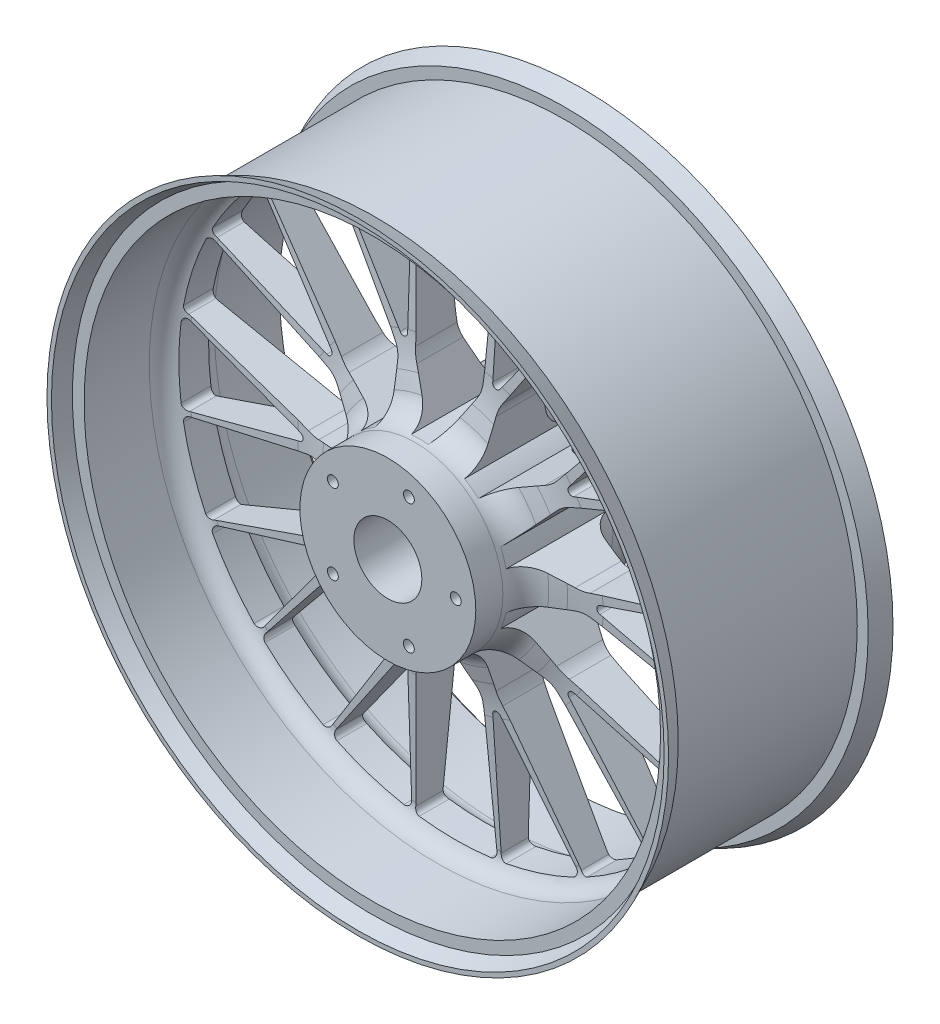
SolidWorks part; units mm, degrees
material "7050-T7651"
ref_plane "Front Plane" through (0, 0, 0) normal (0, 0, 1) x (1, 0, 0)
ref_plane "Top Plane" through (0, 0, 0) normal (0, 1, 0) x (1, 0, 0)
ref_plane "Right Plane" through (0, 0, 0) normal (1, 0, 0) x (0, 0, -1)
sketch "Sketch1" plane through (0, 0, 0) normal (0, 0, 1) x (1, 0, 0)
  line L0 (0, 0) -> (0, 203.2) construction
  line L1 (-29.8081, 197.311) -> (-24.756, 100.9121)
  line L2 (-22.1039, 91.9588) -> (-6.3592, 64.6882)
  line L3 (91.8613, 177.1487) -> (39.2866, 96.1908)
  line L4 (22.1039, 91.9588) -> (6.3592, 64.6882)
  line L5 (29.8081, 197.311) -> (24.756, 100.9121)
  line L6 (0, 0) -> (-75.5575, 232.5421) construction
  line L7 (-31.3013, 105.6196) -> (-32.8759, 195.8269)
  line L8 (-36.7583, 103.8465) -> (-88.471, 177.7703)
  line L9 (36.1696, 87.3886) -> (32.878, 56.0717)
  line L10 (71.9345, 61.4039) -> (43.1675, 48.596)
  line L11 (140.0918, 142.1072) -> (79.3427, 67.0884)
  line L12 (36.7583, 103.8465) -> (88.507, 177.7513)
  line L13 (31.3013, 105.6196) -> (32.9162, 195.8211)
  line L14 (0, 0) -> (119.438, 164.3923) construction
  line L15 (0, 0) -> (75.5575, 232.5421) construction
  line L16 (178.4427, 89.3216) -> (88.3231, 54.7279)
  line L17 (80.6276, 49.4389) -> (59.557, 26.0377)
  line L18 (94.2886, 7.3948) -> (63.4872, 13.9418)
  line L19 (196.8651, 32.6233) -> (103.6232, 7.6392)
  line L20 (90.7776, 62.4076) -> (176.0833, 91.7807)
  line L21 (87.405, 67.0496) -> (141.7305, 139.075)
  line L22 (0, 0) -> (193.2547, 62.7923) construction
  line L23 (0, 0) -> (197.8121, 143.7189) construction
  line L24 (196.8651, -32.6233) -> (103.6232, -7.6392)
  line L25 (94.2886, -7.3948) -> (63.4872, -13.9418)
  line L26 (80.6276, -49.4389) -> (59.557, -26.0377)
  line L27 (178.4427, -89.3216) -> (88.3231, -54.7279)
  line L28 (110.1229, -2.8689) -> (196.4017, -29.247)
  line L29 (110.1229, 2.8689) -> (196.4086, 29.2069)
  line L30 (0, 0) -> (193.2547, -62.7923) construction
  line L31 (0, 0) -> (244.5092, 0) construction
  line L32 (140.0918, -142.1072) -> (79.3427, -67.0884)
  line L33 (71.9345, -61.4039) -> (43.1675, -48.596)
  line L34 (36.1696, -87.3886) -> (32.878, -56.0717)
  line L35 (91.8613, -177.1487) -> (39.2866, -96.1908)
  line L36 (87.405, -67.0496) -> (141.7014, -139.1033)
  line L37 (90.7776, -62.4076) -> (176.0653, -91.8172)
  line L38 (0, 0) -> (119.438, -164.3923) construction
  line L39 (0, 0) -> (197.8121, -143.7189) construction
  line L40 (29.8081, -197.311) -> (24.756, -100.9121)
  line L41 (22.1039, -91.9588) -> (6.3592, -64.6882)
  line L42 (-22.1039, -91.9588) -> (-6.3592, -64.6882)
  line L43 (-29.8081, -197.311) -> (-24.756, -100.9121)
  line L44 (31.3013, -105.6196) -> (32.8759, -195.8269)
  line L45 (36.7583, -103.8465) -> (88.471, -177.7703)
  line L46 (0, 0) -> (0, -203.2) construction
  line L47 (0, 0) -> (75.5575, -232.5421) construction
  line L48 (-91.8613, -177.1487) -> (-39.2866, -96.1908)
  line L49 (-36.1696, -87.3886) -> (-32.878, -56.0717)
  line L50 (-71.9345, -61.4039) -> (-43.1675, -48.596)
  line L51 (-140.0918, -142.1072) -> (-79.3427, -67.0884)
  line L52 (-36.7583, -103.8465) -> (-88.507, -177.7513)
  line L53 (-31.3013, -105.6196) -> (-32.9162, -195.8211)
  line L54 (0, 0) -> (-119.438, -164.3923) construction
  line L55 (0, 0) -> (-75.5575, -232.5421) construction
  line L56 (-178.4427, -89.3216) -> (-88.3231, -54.7279)
  line L57 (-80.6276, -49.4389) -> (-59.557, -26.0377)
  line L58 (-94.2886, -7.3948) -> (-63.4872, -13.9418)
  line L59 (-196.8651, -32.6233) -> (-103.6232, -7.6392)
  line L60 (-90.7776, -62.4076) -> (-176.0833, -91.7807)
  line L61 (-87.405, -67.0496) -> (-141.7305, -139.075)
  line L62 (0, 0) -> (-193.2547, -62.7923) construction
  line L63 (0, 0) -> (-197.8121, -143.7189) construction
  line L64 (-196.8651, 32.6233) -> (-103.6232, 7.6392)
  line L65 (-94.2886, 7.3948) -> (-63.4872, 13.9418)
  line L66 (-80.6276, 49.4389) -> (-59.557, 26.0377)
  line L67 (-178.4427, 89.3216) -> (-88.3231, 54.7279)
  line L68 (-110.1229, 2.8689) -> (-196.4017, 29.247)
  line L69 (-110.1229, -2.8689) -> (-196.4086, -29.2069)
  line L70 (0, 0) -> (-193.2547, 62.7923) construction
  line L71 (0, 0) -> (-244.5092, 0) construction
  line L72 (-140.0918, 142.1072) -> (-79.3427, 67.0884)
  line L73 (-71.9345, 61.4039) -> (-43.1675, 48.596)
  line L74 (-36.1696, 87.3886) -> (-32.878, 56.0717)
  line L75 (-91.8613, 177.1487) -> (-39.2866, 96.1908)
  line L76 (-87.405, 67.0496) -> (-141.7014, 139.1033)
  line L77 (-90.7776, 62.4076) -> (-176.0653, 91.8172)
  line L78 (0, 0) -> (-119.438, 164.3923) construction
  line L79 (0, 0) -> (-197.8121, 143.7189) construction
  circle A0 centre (0, 0) radius 25
  arc A1 (26.3319, 201.4867) -> (-26.3319, 201.4867) centre (0, 0) ccw
  arc A2 (6.3592, 64.6882) -> (-6.3592, 64.6882) centre (0, 0) ccw
  arc A3 (-31.3013, 105.6196) -> (-33.3738, 102.7141) centre (-34.3009, 105.5673) cw
  arc A4 (-36.7583, 103.8465) -> (-33.3738, 102.7141) centre (-34.3009, 105.5673) ccw
  arc A5 (22.1039, 91.9588) -> (24.756, 100.9121) centre (4.7834, 101.9588) ccw
  arc A6 (-24.756, 100.9121) -> (-22.1039, 91.9588) centre (-4.7834, 101.9588) ccw
  arc A7 (-37.6158, 199.688) -> (-86.9041, 183.6788) centre (0, 0) ccw
  arc A8 (29.8081, 197.311) -> (26.3319, 201.4867) centre (25.8136, 197.5204) ccw
  arc A9 (-29.8081, 197.311) -> (-26.3319, 201.4867) centre (-25.8136, 197.5204) cw
  arc A10 (-32.8759, 195.8269) -> (-37.6158, 199.688) centre (-36.8753, 195.7571) ccw
  arc A11 (-88.471, 177.7703) -> (-86.9041, 183.6788) centre (-85.1934, 180.0631) cw
  arc A12 (139.7338, 147.5286) -> (97.1279, 178.4836) centre (0, 0) ccw
  arc A13 (43.1675, 48.596) -> (32.878, 56.0717) centre (0, 0) ccw
  arc A14 (36.7583, 103.8465) -> (33.3738, 102.7141) centre (34.3009, 105.5673) cw
  arc A15 (31.3013, 105.6196) -> (33.3738, 102.7141) centre (34.3009, 105.5673) ccw
  arc A16 (71.9345, 61.4039) -> (79.3427, 67.0884) centre (63.7998, 79.6748) ccw
  arc A17 (39.2866, 96.1908) -> (36.1696, 87.3886) centre (56.06, 85.2981) ccw
  arc A18 (86.9419, 183.661) -> (37.6568, 199.6803) centre (0, 0) ccw
  arc A19 (140.0918, 142.1072) -> (139.7338, 147.5286) centre (136.9832, 144.6245) ccw
  arc A20 (91.8613, 177.1487) -> (97.1279, 178.4836) centre (95.216, 174.9702) cw
  arc A21 (88.507, 177.7513) -> (86.9419, 183.661) centre (85.2304, 180.0456) ccw
  arc A22 (32.9162, 195.8211) -> (37.6568, 199.6803) centre (36.9156, 195.7495) cw
  arc A23 (199.7622, 37.2197) -> (183.4882, 87.3059) centre (0, 0) ccw
  arc A24 (63.4872, 13.9418) -> (59.557, 26.0377) centre (0, 0) ccw
  arc A25 (90.7776, 62.4076) -> (87.3738, 63.4808) centre (89.8009, 65.2442) cw
  arc A26 (87.405, 67.0496) -> (87.3738, 63.4808) centre (89.8009, 65.2442) ccw
  arc A27 (94.2886, 7.3948) -> (103.6232, 7.6392) centre (98.4468, 26.9577) ccw
  arc A28 (88.3231, 54.7279) -> (80.6276, 49.4389) centre (95.4905, 36.0563) ccw
  arc A29 (178.2906, 97.4817) -> (147.8341, 139.4106) centre (0, 0) ccw
  arc A30 (196.8651, 32.6233) -> (199.7622, 37.2197) centre (195.8299, 36.487) ccw
  arc A31 (178.4427, 89.3216) -> (183.4882, 87.3059) centre (179.8762, 85.5873) cw
  arc A32 (176.0833, 91.7807) -> (178.2906, 97.4817) centre (174.781, 95.5628) ccw
  arc A33 (141.7305, 139.075) -> (147.8341, 139.4106) centre (144.924, 136.6663) cw
  arc A34 (183.4882, -87.3059) -> (199.7622, -37.2197) centre (0, 0) ccw
  arc A35 (59.557, -26.0377) -> (63.4872, -13.9418) centre (0, 0) ccw
  arc A36 (110.1229, -2.8689) -> (108, 0) centre (111, 0) cw
  arc A37 (110.1229, 2.8689) -> (108, 0) centre (111, 0) ccw
  arc A38 (80.6276, -49.4389) -> (88.3231, -54.7279) centre (95.4905, -36.0563) ccw
  arc A39 (103.6232, -7.6392) -> (94.2886, -7.3948) centre (98.4468, -26.9577) ccw
  arc A40 (201.5385, -25.9323) -> (201.5438, 25.8908) centre (0, 0) ccw
  arc A41 (178.4427, -89.3216) -> (183.4882, -87.3059) centre (179.8762, -85.5873) ccw
  arc A42 (196.8651, -32.6233) -> (199.7622, -37.2197) centre (195.8299, -36.487) cw
  arc A43 (196.4017, -29.247) -> (201.5385, -25.9323) centre (197.5712, -25.4218) ccw
  arc A44 (196.4086, 29.2069) -> (201.5438, 25.8908) centre (197.5764, 25.3812) cw
  arc A45 (97.1279, -178.4836) -> (139.7338, -147.5286) centre (0, 0) ccw
  arc A46 (32.878, -56.0717) -> (43.1675, -48.596) centre (0, 0) ccw
  arc A47 (87.405, -67.0496) -> (87.3738, -63.4808) centre (89.8009, -65.2442) cw
  arc A48 (90.7776, -62.4076) -> (87.3738, -63.4808) centre (89.8009, -65.2442) ccw
  arc A49 (36.1696, -87.3886) -> (39.2866, -96.1908) centre (56.06, -85.2981) ccw
  arc A50 (79.3427, -67.0884) -> (71.9345, -61.4039) centre (63.7998, -79.6748) ccw
  arc A51 (147.8055, -139.441) -> (178.2706, -97.5184) centre (0, 0) ccw
  arc A52 (91.8613, -177.1487) -> (97.1279, -178.4836) centre (95.216, -174.9702) ccw
  arc A53 (140.0918, -142.1072) -> (139.7338, -147.5286) centre (136.9832, -144.6245) cw
  arc A54 (141.7014, -139.1033) -> (147.8055, -139.441) centre (144.8959, -136.6961) ccw
  arc A55 (176.0653, -91.8172) -> (178.2706, -97.5184) centre (174.7613, -95.5987) cw
  arc A56 (-26.3319, -201.4867) -> (26.3319, -201.4867) centre (0, 0) ccw
  arc A57 (-6.3592, -64.6882) -> (6.3592, -64.6882) centre (0, 0) ccw
  arc A58 (31.3013, -105.6196) -> (33.3738, -102.7141) centre (34.3009, -105.5673) cw
  arc A59 (36.7583, -103.8465) -> (33.3738, -102.7141) centre (34.3009, -105.5673) ccw
  arc A60 (-22.1039, -91.9588) -> (-24.756, -100.9121) centre (-4.7834, -101.9588) ccw
  arc A61 (24.756, -100.9121) -> (22.1039, -91.9588) centre (4.7834, -101.9588) ccw
  arc A62 (37.6158, -199.688) -> (86.9041, -183.6788) centre (0, 0) ccw
  arc A63 (-29.8081, -197.311) -> (-26.3319, -201.4867) centre (-25.8136, -197.5204) ccw
  arc A64 (29.8081, -197.311) -> (26.3319, -201.4867) centre (25.8136, -197.5204) cw
  arc A65 (32.8759, -195.8269) -> (37.6158, -199.688) centre (36.8753, -195.7571) ccw
  arc A66 (88.471, -177.7703) -> (86.9041, -183.6788) centre (85.1934, -180.0631) cw
  arc A67 (-139.7338, -147.5286) -> (-97.1279, -178.4836) centre (0, 0) ccw
  arc A68 (-43.1675, -48.596) -> (-32.878, -56.0717) centre (0, 0) ccw
  arc A69 (-36.7583, -103.8465) -> (-33.3738, -102.7141) centre (-34.3009, -105.5673) cw
  arc A70 (-31.3013, -105.6196) -> (-33.3738, -102.7141) centre (-34.3009, -105.5673) ccw
  arc A71 (-71.9345, -61.4039) -> (-79.3427, -67.0884) centre (-63.7998, -79.6748) ccw
  arc A72 (-39.2866, -96.1908) -> (-36.1696, -87.3886) centre (-56.06, -85.2981) ccw
  arc A73 (-86.9419, -183.661) -> (-37.6568, -199.6803) centre (0, 0) ccw
  arc A74 (-140.0918, -142.1072) -> (-139.7338, -147.5286) centre (-136.9832, -144.6245) ccw
  arc A75 (-91.8613, -177.1487) -> (-97.1279, -178.4836) centre (-95.216, -174.9702) cw
  arc A76 (-88.507, -177.7513) -> (-86.9419, -183.661) centre (-85.2304, -180.0456) ccw
  arc A77 (-32.9162, -195.8211) -> (-37.6568, -199.6803) centre (-36.9156, -195.7495) cw
  arc A78 (-199.7622, -37.2197) -> (-183.4882, -87.3059) centre (0, 0) ccw
  arc A79 (-63.4872, -13.9418) -> (-59.557, -26.0377) centre (0, 0) ccw
  arc A80 (-90.7776, -62.4076) -> (-87.3738, -63.4808) centre (-89.8009, -65.2442) cw
  arc A81 (-87.405, -67.0496) -> (-87.3738, -63.4808) centre (-89.8009, -65.2442) ccw
  arc A82 (-94.2886, -7.3948) -> (-103.6232, -7.6392) centre (-98.4468, -26.9577) ccw
  arc A83 (-88.3231, -54.7279) -> (-80.6276, -49.4389) centre (-95.4905, -36.0563) ccw
  arc A84 (-178.2906, -97.4817) -> (-147.8341, -139.4106) centre (0, 0) ccw
  arc A85 (-196.8651, -32.6233) -> (-199.7622, -37.2197) centre (-195.8299, -36.487) ccw
  arc A86 (-178.4427, -89.3216) -> (-183.4882, -87.3059) centre (-179.8762, -85.5873) cw
  arc A87 (-176.0833, -91.7807) -> (-178.2906, -97.4817) centre (-174.781, -95.5628) ccw
  arc A88 (-141.7305, -139.075) -> (-147.8341, -139.4106) centre (-144.924, -136.6663) cw
  arc A89 (-183.4882, 87.3059) -> (-199.7622, 37.2197) centre (0, 0) ccw
  arc A90 (-59.557, 26.0377) -> (-63.4872, 13.9418) centre (0, 0) ccw
  arc A91 (-110.1229, 2.8689) -> (-108, 0) centre (-111, 0) cw
  arc A92 (-110.1229, -2.8689) -> (-108, 0) centre (-111, 0) ccw
  arc A93 (-80.6276, 49.4389) -> (-88.3231, 54.7279) centre (-95.4905, 36.0563) ccw
  arc A94 (-103.6232, 7.6392) -> (-94.2886, 7.3948) centre (-98.4468, 26.9577) ccw
  arc A95 (-201.5385, 25.9323) -> (-201.5438, -25.8908) centre (0, 0) ccw
  arc A96 (-178.4427, 89.3216) -> (-183.4882, 87.3059) centre (-179.8762, 85.5873) ccw
  arc A97 (-196.8651, 32.6233) -> (-199.7622, 37.2197) centre (-195.8299, 36.487) cw
  arc A98 (-196.4017, 29.247) -> (-201.5385, 25.9323) centre (-197.5712, 25.4218) ccw
  arc A99 (-196.4086, -29.2069) -> (-201.5438, -25.8908) centre (-197.5764, -25.3812) cw
  arc A100 (-97.1279, 178.4836) -> (-139.7338, 147.5286) centre (0, 0) ccw
  arc A101 (-32.878, 56.0717) -> (-43.1675, 48.596) centre (0, 0) ccw
  arc A102 (-87.405, 67.0496) -> (-87.3738, 63.4808) centre (-89.8009, 65.2442) cw
  arc A103 (-90.7776, 62.4076) -> (-87.3738, 63.4808) centre (-89.8009, 65.2442) ccw
  arc A104 (-36.1696, 87.3886) -> (-39.2866, 96.1908) centre (-56.06, 85.2981) ccw
  arc A105 (-79.3427, 67.0884) -> (-71.9345, 61.4039) centre (-63.7998, 79.6748) ccw
  arc A106 (-147.8055, 139.441) -> (-178.2706, 97.5184) centre (0, 0) ccw
  arc A107 (-91.8613, 177.1487) -> (-97.1279, 178.4836) centre (-95.216, 174.9702) ccw
  arc A108 (-140.0918, 142.1072) -> (-139.7338, 147.5286) centre (-136.9832, 144.6245) cw
  arc A109 (-141.7014, 139.1033) -> (-147.8055, 139.441) centre (-144.8959, 136.6961) ccw
  arc A110 (-176.0653, 91.8172) -> (-178.2706, 97.5184) centre (-174.7613, 95.5987) cw
  circle A111 centre (0, 0) radius 228.6
  circle A112 centre (0, 0) radius 50 construction
  circle A113 centre (15.4508, 47.5528) radius 4
  circle A114 centre (50, 0) radius 4
  circle A115 centre (15.4508, -47.5528) radius 4
  circle A116 centre (-40.4508, -29.3893) radius 4
  circle A117 centre (-40.4508, 29.3893) radius 4
  point P11 (0, 53.8255)
  point P23 (24.5047, 96.1171)
  point P26 (-24.5047, 96.1171)
  point P27 (30, 200.9732)
  point P30 (-30, 200.9732)
  point P33 (-33, 200.5025)
  point P36 (-91.1548, 181.6068)
  point P48 (31.6378, 43.5457)
  point P77 (51.1911, 16.633)
  point P106 (51.1911, -16.633)
  point P135 (31.6378, -43.5457)
  point P164 (0, -53.8255)
  point P193 (-31.6378, -43.5457)
  point P222 (-51.1911, -16.633)
  point P251 (-51.1911, 16.633)
  point P280 (-31.6378, 43.5457)
  dimension "D1" = 50
  dimension "D2" = 406.4
  dimension "D3" = 130
  dimension "D11" = 3
  dimension "D12" = 20
  dimension "D13" = 4
  dimension "D15" = 457.2
  dimension "D16" = 100
  dimension "D17" = 8
  dimension "D19" = 108
  dimension "D4" = 6
  dimension "D5" = 105
  dimension "D6" = 60
  dimension "D7" = 3
  dimension "D8" = 18
  dimension "D9" = 30
  dimension "D10" = 2
  dimension "D14" = 10
  dimension "D18" = 5
extrude "Boss-Extrude1" add sketch "Sketch1" along normal mid plane 165.1
sketch "Sketch2" plane through (0, 0, 0) normal (1, 0, 0) x (0, 0, -1)
  line L0 (0, 0) -> (0, 217.623) construction
  line L1 (-10, 197.311) -> (-14.4558, 112.2901)
  line L2 (-82.55, 100.9121) -> (82.55, 100.9121) construction
  line L3 (-82.55, 228.6) -> (82.55, 228.6)
  line L4 (-82.55, 197.311) -> (82.55, 197.311) construction
  line L5 (-71.85, 212) -> (-23.9393, 212)
  line L6 (-82.55, 228.6) -> (-82.55, -228.6) construction
  line L8 (-18.1925, 89.9599) -> (-21.2849, 79.1754)
  line L9 (-82.55, 64.6882) -> (82.55, 64.6882) construction
  line L10 (-40.5102, 64.6882) -> (-82.55, 64.6882)
  line L11 (-82.55, 64.6882) -> (-82.55, 225.3213)
  line L12 (71.85, 220.6032) -> (71.85, 212)
  line L13 (40.5102, 64.6882) -> (82.55, 64.6882)
  line L14 (18.1925, 89.9599) -> (21.2849, 79.1754)
  line L15 (82.55, 225.3213) -> (71.85, 220.6032)
  line L16 (10, 197.311) -> (14.4558, 112.2901)
  line L17 (0, 0) -> (30.7585, 0) construction
  line L18 (-69.85, 215) -> (69.85, 215)
  line L20 (-69.85, 215) -> (-69.85, 223)
  line L21 (-69.85, 223) -> (-82.55, 228.6)
  line L22 (-82.55, 225.3213) -> (-71.85, 220.6032)
  line L23 (-71.85, 220.6032) -> (-71.85, 212)
  line L24 (69.85, 223) -> (82.55, 228.6)
  line L25 (69.85, 215) -> (69.85, 223)
  line L26 (82.55, 64.6882) -> (82.55, 225.3213)
  line L27 (71.85, 212) -> (23.9393, 212)
  arc A0 (-23.9393, 212) -> (-10, 197.311) centre (-23.9393, 198.0416) cw
  arc A1 (23.9393, 212) -> (10, 197.311) centre (23.9393, 198.0416) ccw
  arc A2 (40.5102, 64.6882) -> (21.2849, 79.1754) centre (40.5102, 84.6882) cw
  arc A3 (-21.2849, 79.1754) -> (-40.5102, 64.6882) centre (-40.5102, 84.6882) cw
  arc A4 (18.1925, 89.9599) -> (14.4558, 112.2901) centre (114.3187, 117.5237) cw
  arc A5 (-14.4558, 112.2901) -> (-18.1925, 89.9599) centre (-114.3187, 117.5237) cw
  point P5 (0, 228.6)
  point P31 (25.4391, 64.6882)
  point P34 (-25.4391, 64.6882)
  point P37 (15.0521, 100.9121)
  point P40 (-15.0521, 100.9121)
  point P45 (0, 215)
  dimension "D5" = 20
  dimension "D6" = 100
  dimension "D1" = 3
  dimension "D2" = 20
  dimension "D3" = 212
  dimension "D4" = 16
  dimension "D7" = 139.7
  dimension "D8" = 3
  dimension "D9" = 228.6
  dimension "D10" = 3
  dimension "D11" = 2
  dimension "D13" = 8
revolve "Cut-Revolve1" cut sketch "Sketch2" angle 360 about L17
sketch "Croquis1" plane through (0, 0, 82.55) normal (0, 0, 1) x (1, 0, 0)
  circle A1 centre (0, 0) radius 64.6882
  circle A2 centre (0, 0) radius 64.6882
  dimension "D1" = 0
extrude "Cortar-Extruir1" cut sketch "Croquis1" against normal blind 22.125 contours A2
sketch "Croquis2" plane through (0, 0, -82.55) normal (0, 0, -1) x (-1, 0, 0)
  circle A1 centre (0, 0) radius 64.6882
  circle A2 centre (0, 0) radius 64.6882
  dimension "D1" = 0
extrude "Cortar-Extruir2" cut sketch "Croquis2" against normal blind 22.125
